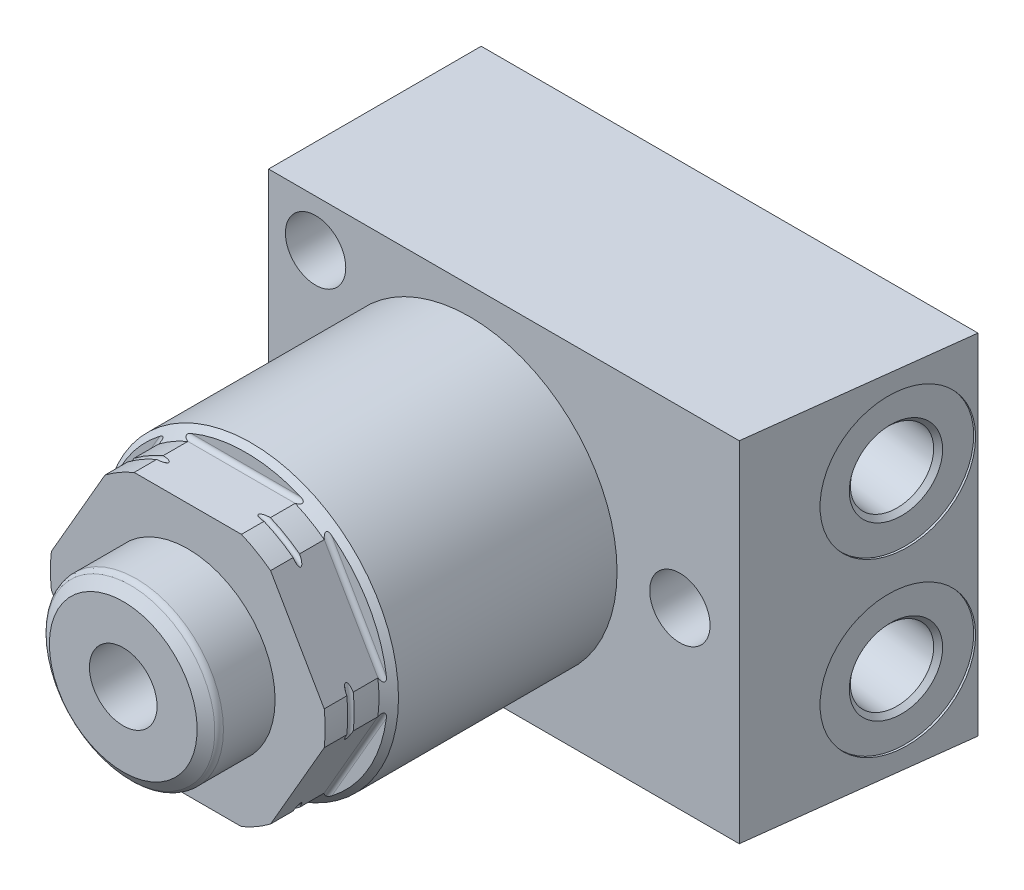
SolidWorks part; units mm, degrees
material "Alloy Steel"
ref_plane "Front Plane" through (0, 0, 0) normal (0, 0, 1) x (1, 0, 0)
ref_plane "Top Plane" through (0, 0, 0) normal (0, 1, 0) x (1, 0, 0)
ref_plane "Right Plane" through (0, 0, 0) normal (1, 0, 0) x (0, 0, -1)
sketch "Sketch1" plane through (0, 0, 0) normal (1, 0, 0) x (0, 0, -1)
  line L0 (0, 0) -> (122.3375, 0) construction
  line L1 (0, 0) -> (0, 13.9954)
  line L2 (0, 13.9954) -> (-4.6736, 13.9954)
  line L3 (-4.6736, 13.9954) -> (-4.6736, 15.5067)
  line L6 (-4.6736, 15.5067) -> (-8.2804, 15.5067)
  line L7 (-8.2804, 15.5067) -> (-10.1854, 17.4117)
  line L8 (-10.1854, 17.4117) -> (-42.2275, 17.4117)
  line L9 (-42.2275, 17.4117) -> (-43.3832, 16.256)
  line L10 (-43.3832, 16.256) -> (-49.7332, 16.256)
  line L11 (-49.7332, 16.256) -> (-49.7332, 0)
  line L12 (0, 0) -> (-49.7332, 0)
  dimension "D1" = 27.9908
  dimension "D2" = 4.6736
  dimension "D5" = 31.0134
  dimension "D6" = 8.2804
  dimension "D7" = 34.8234
  dimension "D8" = 45
  dimension "D9" = 49.7332
  dimension "D10" = 32.512
  dimension "D11" = 45
  dimension "D12" = 6.35
revolve "Revolve1" add sketch "Sketch1" angle 360 about L0
sketch "Sketch2" plane through (0, 0, 0) normal (1, 0, 0) x (0, 0, -1)
  line L0 (0, 0) -> (-47.105, 0) construction
  line L1 (-49.7332, 14.9669) -> (-43.3832, 14.9669)
  line L2 (-49.7332, 16.256) -> (-49.7332, -16.256) construction
  line L3 (-42.8752, 15.4749) -> (-42.8752, 18.1419)
  line L4 (-42.8752, 18.1419) -> (-49.7332, 18.1419)
  line L5 (-49.7332, 18.1419) -> (-49.7332, 14.9669)
  arc A0 (-42.8752, 15.4749) -> (-43.3832, 14.9669) centre (-43.3832, 15.4749) cw
  dimension "D4" = 0.508
  dimension "D1" = 29.9339
  dimension "D2" = 6.858
  dimension "D3" = 3.175
extrude "Cut-Extrude1" cut sketch "Sketch2" against normal through all and the other way through all
pattern_circular "CirPattern1" count 6 over 360 about axis through (0, 0, 0) along (0, 0, 1) of "Cut-Extrude1"
sketch "Sketch6" plane through (0, 0, 0) normal (0, 1, 0) x (1, 0, 0)
  line L0 (-23.7998, -16.383) -> (31.8629, -16.383)
  line L1 (31.8629, -16.383) -> (34.9504, 8.763)
  line L2 (34.9504, 8.763) -> (-23.7998, 8.763)
  line L3 (-23.7998, 8.763) -> (-23.7998, -16.383)
  line L4 (6.3441, -49.7332) -> (-6.3441, -49.7332) construction
  dimension "D1" = 33.3502
  dimension "D2" = 83
  dimension "D3" = 25.146
  dimension "D4" = 58.7502
  dimension "D5" = 23.7998
extrude "Extrude1" add sketch "Sketch6" along normal mid plane 41.275
sketch "Sketch3" plane through (0, 0, 0) normal (1, 0, 0) x (0, 0, -1)
  line L0 (0, 0) -> (-60.8041, 0) construction
  line L1 (-57.3659, 0) -> (-57.3659, 8.7376)
  line L2 (-55.8419, 10.3251) -> (-49.7332, 10.3251)
  line L3 (-49.7332, 1.9893) -> (-49.7332, 12.9776) construction
  line L4 (-49.7332, 10.3251) -> (-49.7332, 0)
  line L5 (-49.7332, 1.9893) -> (-49.7332, -1.9893) construction
  line L6 (-49.7332, 0) -> (-57.3659, 0)
  line L8 (-57.3659, 8.7376) -> (-56.5104, 9.9746)
  line L9 (8.763, 20.6375) -> (8.763, -20.6375) construction
  arc A0 (-55.8419, 10.3251) -> (-56.5104, 9.9746) centre (-55.8419, 9.5123) ccw
  dimension "D1" = 0.8128
  dimension "D2" = 20.6502
  dimension "D3" = 66.1289
  dimension "D4" = 1.524
  dimension "D5" = 17.4752
revolve "Revolve2" add sketch "Sketch3" angle 360 about L0
sketch "Sketch4" plane through (0, 0, 57.3659) normal (0, 0, 1) x (1, 0, 0)
  circle A0 centre (0, 0) radius 4.0005
  circle A1 centre (0, 0) radius 10.3251 construction
  dimension "D1" = 8.001
extrude "Cut-Extrude2" cut sketch "Sketch4" against normal blind 6.0452
sketch "Sketch5" plane through (0, 0, 0) normal (1, 0, 0) x (0, 0, -1)
  line L0 (-49.7332, 14.9669) -> (-49.7332, 12.9776) construction
  line L1 (0, 0) -> (-52.6213, 0) construction
  line L2 (-47.0662, 19.431) -> (-47.0662, 16.256)
  line L3 (-46.3042, 19.431) -> (-46.3042, 16.256)
  line L4 (-47.0662, 19.431) -> (-46.3042, 19.431)
  arc A0 (-47.0662, 16.256) -> (-46.3042, 16.256) centre (-46.6852, 16.256) ccw
  dimension "D3" = 0.762
  dimension "D1" = 3.048
  dimension "D2" = 16.256
  dimension "D4" = 3.175
revolve "Cut-Revolve1" cut sketch "Sketch5" angle 360 about L1
hole_wizard "Hole1" positions "Sketch8" profile "Sketch7" legacy end condition up to next
sketch "Sketch8" plane through (0, 0, 16.383) normal (0, 0, 1) x (1, 0, 0)
  line L0 (0, 0) -> (0, 25.169) construction
  line L1 (0, 0) -> (-25.7102, 0) construction
  point P0 (-18.2372, 15.0876)
  point P9 (-18.2372, -15.0876)
  point P10 (24.8412, 0)
  dimension "D1" = 15.0876
  dimension "D2" = 18.2372
  dimension "D3" = 24.8412
sketch "Sketch7" plane through (-18.2372, 15.0876, 16.383) normal (1, 0, 0) x (0, -1, 0)
  line L0 (0, 0) -> (0, 25.146)
  line L1 (0, 25.146) -> (3.5687, 25.146)
  line L2 (3.5687, 25.146) -> (3.5687, 0)
  line L3 (3.5687, 0) -> (0, 0)
  line L4 (0, 110) -> (0, -10) construction
  dimension "Diameter" = 7.1374
  dimension "Depth" = 25.146
ref_plane "Plane1" through (0, -10.1473, 0) normal (0, 1, 0) x (-1, 0, 0)
sketch "Sketch9" plane through (0, -10.1473, 0) normal (0, 1, 0) x (-1, 0, 0)
  line L0 (-33.9134, -0.3174) -> (-18.7621, -2.1778) construction
  line L1 (-31.8629, 16.383) -> (-34.9504, -8.763) construction
  line L2 (-32.9074, 7.876) -> (-32.6553, 7.8451)
  line L3 (-32.6553, 7.8451) -> (-33.0577, 4.5677)
  line L4 (-33.0577, 4.5677) -> (-32.5933, 3.9733)
  line L5 (-32.5933, 3.9733) -> (-22.6351, 2.7506)
  line L6 (-22.6351, 2.7506) -> (-23.1737, -1.6361)
  line L7 (-23.1737, -1.6361) -> (-33.9134, -0.3174)
  line L8 (-33.9134, -0.3174) -> (-32.9074, 7.876)
  dimension "D1" = 8.509
  dimension "D2" = 16.51
  dimension "D3" = 0.254
  dimension "D4" = 8.8392
  dimension "D5" = 10.5664
  dimension "D6" = 45
  dimension "D7" = 9.906
revolve "Cut-Revolve2" cut sketch "Sketch9" angle 360 about L0
pattern_linear "LPattern1" count 2 spacing 20.2946 along (0, 1, 0) of "Cut-Revolve2"
